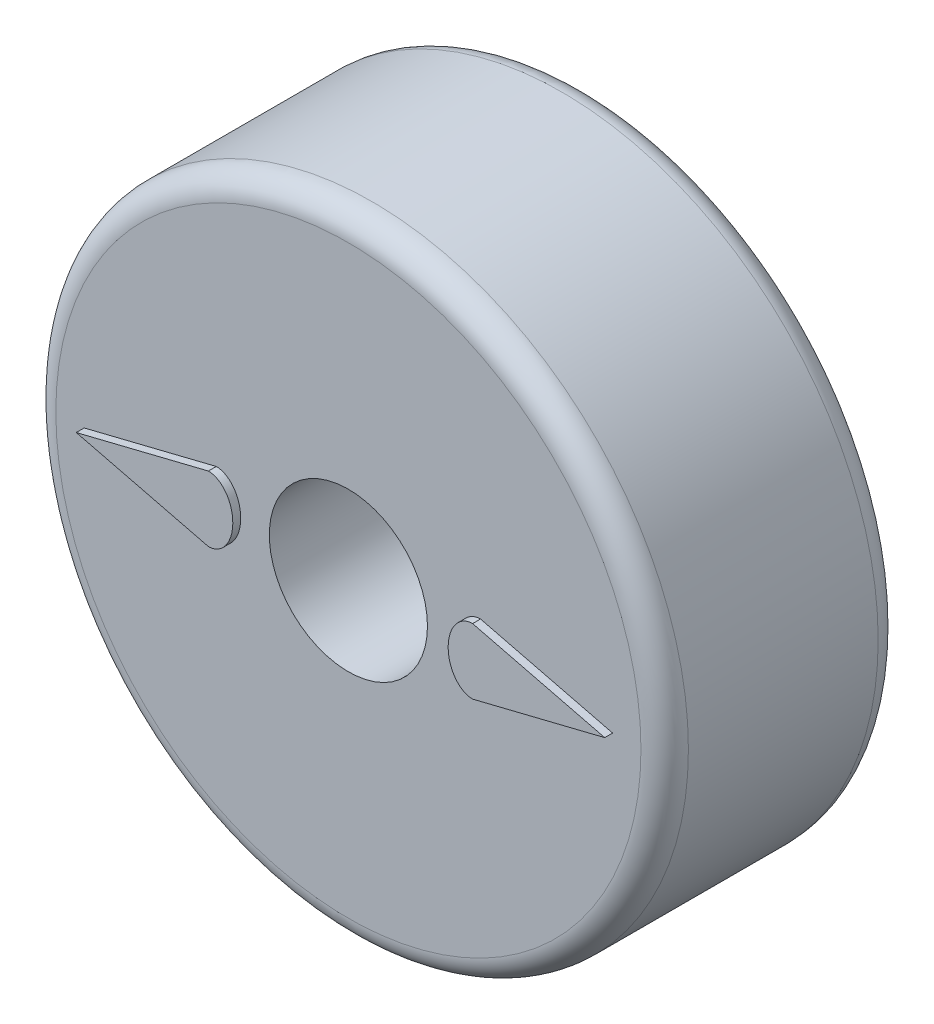
SolidWorks part; units mm, degrees
material "BUTYL"
ref_plane "Front Plane" through (0, 0, 0) normal (0, 0, 1) x (1, 0, 0)
ref_plane "Top Plane" through (0, 0, 0) normal (0, 1, 0) x (1, 0, 0)
ref_plane "Right Plane" through (0, 0, 0) normal (1, 0, 0) x (0, 0, -1)
sketch "Sketch1" plane through (0, 0, 0) normal (0, 0, 1) x (1, 0, 0)
  circle A0 centre (0, 0) radius 101.6
  circle A1 centre (0, 0) radius 25.4
  dimension "D1" = 203.2
  dimension "D2" = 50.8
extrude "Boss-Extrude1" add sketch "Sketch1" along normal blind 76.2
fillet "Fillet1" radius 7.62 2 edges at (101.6, 0, 0) (101.6, 0, 76.2)
sketch "Sketch2" plane through (0, 0, 76.2) normal (0, 0, 1) x (1, 0, 0)
  line L0 (0, 0) -> (84.8726, 0)
  line L1 (84.8726, 0) -> (42.4363, 10.504)
  line L2 (84.8726, 0) -> (42.4363, -10.504)
  ellipse E0 centre (42.4363, 0) end of major axis (42.4363, 10.504) minor radius 7.849 (42.4363, 10.504) -> (42.4363, -10.504) ccw
extrude "Boss-Extrude2" add sketch "Sketch2" along normal blind 2.54 contours L1 E0 L0 | L0 E0 L2
mirror "Mirror1" about plane through (0, 0, 0) normal (1, 0, 0) of "Boss-Extrude2"
